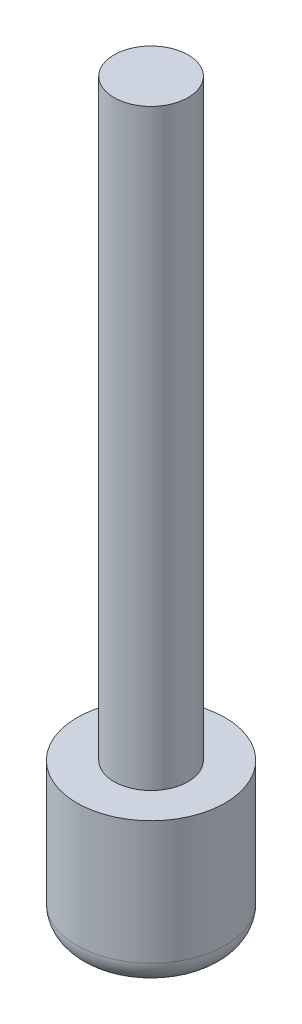
SolidWorks part; units mm, degrees
ref_plane "Front Plane" through (0, 0, 0) normal (0, 0, 1) x (1, 0, 0)
ref_plane "Top Plane" through (0, 0, 0) normal (0, 1, 0) x (1, 0, 0)
ref_plane "Right Plane" through (0, 0, 0) normal (1, 0, 0) x (0, 0, -1)
sketch "Sketch1" plane through (0, 0, 0) normal (0, 0, 1) x (1, 0, 0)
  line L1 (0, 0) -> (50.8, 0)
  line L2 (0, 0) -> (0, 152.4)
  line L3 (38.1, 152.4) -> (76.2, 152.4)
  line L4 (76.2, 25.4) -> (76.2, 152.4)
  line L6 (0, 152.4) -> (0, 762)
  line L7 (0, 762) -> (38.1, 762)
  line L8 (38.1, 152.4) -> (38.1, 762)
  arc A0 (76.2, 25.4) -> (50.8, 0) centre (50.8, 25.4) cw
  point P7 (76.2, 0)
  dimension "D3" = 25.4
  dimension "D1" = 76.2
  dimension "D2" = 152.4
  dimension "D4" = 609.6
  dimension "D5" = 38.1
revolve "Revolve1" add sketch "Sketch1" angle 360 about L6
